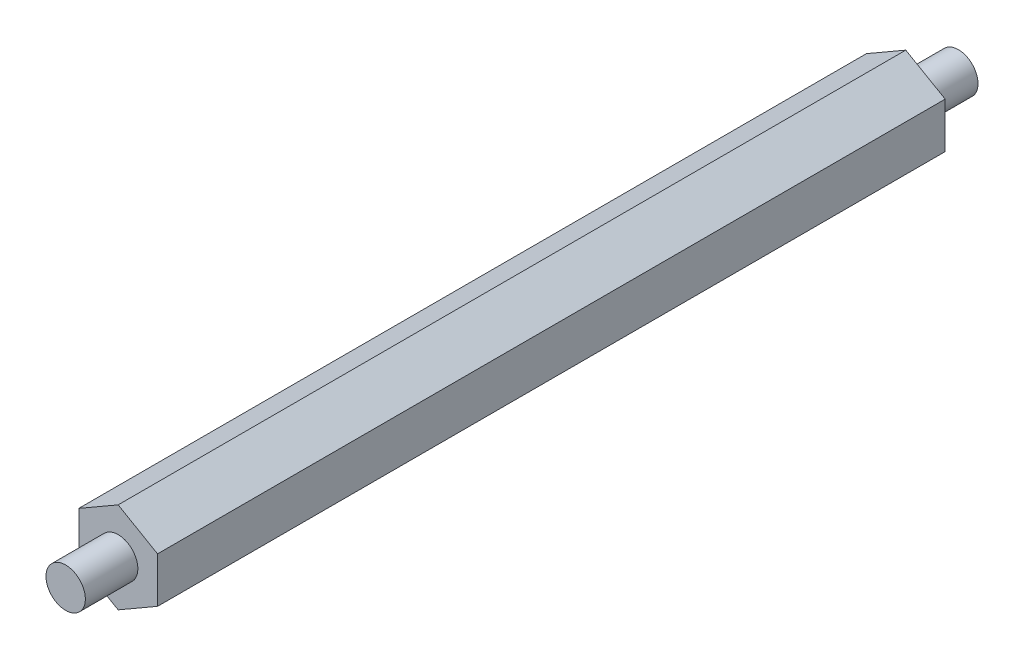
SolidWorks part; units mm, degrees
material "Nylon 6/10"
ref_plane "Front Plane" through (0, 0, 0) normal (0, 0, 1) x (1, 0, 0)
ref_plane "Top Plane" through (0, 0, 0) normal (0, 1, 0) x (1, 0, 0)
ref_plane "Right Plane" through (0, 0, 0) normal (1, 0, 0) x (0, 0, -1)
sketch "Sketch1" plane through (0, 0, 0) normal (0, 0, 1) x (1, 0, 0)
  line L1 (-0.9186, -3.3315) -> (2.0814, -1.5995)
  line L2 (2.0814, -1.5995) -> (2.0814, 1.8646)
  line L3 (2.0814, 1.8646) -> (-0.9186, 3.5967)
  line L4 (-0.9186, 3.5967) -> (-3.9186, 1.8646)
  line L5 (-3.9186, 1.8646) -> (-3.9186, -1.5995)
  line L6 (-3.9186, -1.5995) -> (-0.9186, -3.3315)
  circle A0 centre (-0.9186, 0.1326) radius 3 construction
  dimension "D1" = 6
extrude "Boss-Extrude1" add sketch "Sketch1" along normal blind 60 contours L4 L5 L6 L1 L2 L3
sketch "Sketch2" plane through (0, 0, 60) normal (0, 0, 1) x (1, 0, 0)
  circle A0 centre (-0.9186, 0.1326) radius 1.5
extrude "Boss-Extrude2" add sketch "Sketch2" along normal blind 4
sketch "Sketch3" plane through (0, 0, 0) normal (0, 0, -1) x (-1, 0, 0)
  circle A0 centre (0.9186, 0.1326) radius 1.5
extrude "Boss-Extrude3" add sketch "Sketch3" along normal blind 4
